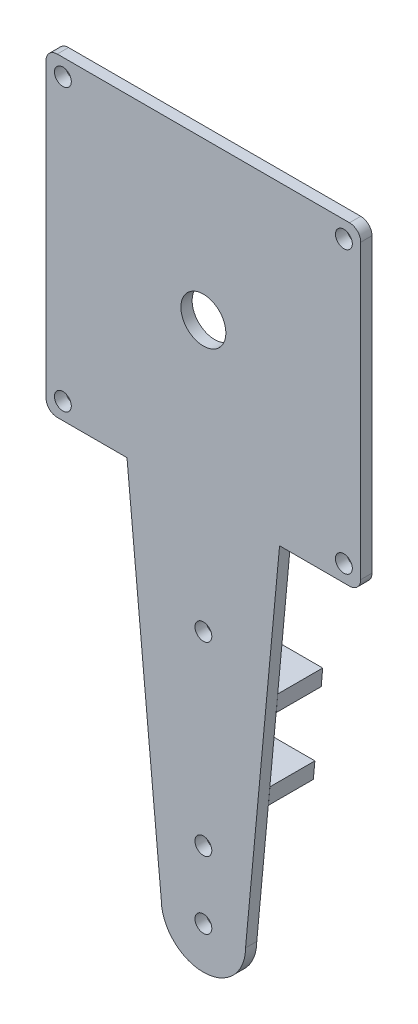
SolidWorks part; units mm, degrees
material "6061 Alloy"
ref_plane "Front Plane" through (0, 0, 0) normal (0, 0, 1) x (1, 0, 0)
ref_plane "Top Plane" through (0, 0, 0) normal (0, 1, 0) x (1, 0, 0)
ref_plane "Right Plane" through (0, 0, 0) normal (1, 0, 0) x (0, 0, -1)
sketch "Sketch2" plane through (0, 0, 0) normal (0, 0, 1) x (1, 0, 0)
  line L0 (-13.5937, -28) -> (-26, -28)
  line L1 (26, 28) -> (-26, 28)
  line L2 (28, 26) -> (28, -26)
  line L3 (26, -28) -> (13.5557, -28)
  line L4 (-28, 26) -> (-28, -26)
  line L5 (28, 28) -> (-28, -28) construction
  line L6 (28, -28) -> (-28, 28) construction
  line L13 (-7.5, -93) -> (7.5, -93)
  line L15 (-7.5, -93) -> (-13.5937, -28)
  line L16 (-14.976, -13.2559) -> (-12.375, -41) construction
  line L17 (7.5, -93) -> (13.5557, -28)
  circle A2 centre (25, 25) radius 1.5
  circle A3 centre (25, -25) radius 1.5
  circle A4 centre (-25, -25) radius 1.5
  circle A5 centre (-25, 25) radius 1.5
  arc A6 (28, 26) -> (26, 28) centre (26, 26) ccw
  arc A7 (28, -26) -> (26, -28) centre (26, -26) cw
  arc A8 (-26, -28) -> (-28, -26) centre (-26, -26) cw
  arc A9 (-28, 26) -> (-26, 28) centre (-26, 26) cw
  point P0 (0, 0)
  point P17 (0, 0)
  dimension "D1" = 56
  dimension "D2" = 56
  dimension "D3" = 25
  dimension "D4" = 3
  dimension "D6" = 2
  dimension "D7" = 2
  dimension "D8" = 65
  dimension "D9" = 15
  dimension "D10" = 7.5
  dimension "D5" = 4
extrude "Boss-Extrude1" add sketch "Sketch2" along normal blind 2
sketch "Sketch3" plane through (0, 0, 2) normal (0, 0, 1) x (1, 0, 0)
  circle A0 centre (0, 0) radius 4
  dimension "D1" = 8
extrude "Cut-Extrude1" cut sketch "Sketch3" against normal blind 10
sketch "Sketch4" plane through (0, 0, 0) normal (0, 0, -1) x (-1, 0, 0)
  line L0 (-11.2266, -53) -> (-10.9688, -56)
  line L1 (-7.5, -93) -> (-13.5557, -28) construction
  line L2 (11.25, -53) -> (-11.25, -53) construction
  line L3 (-10.9688, -56) -> (10.9687, -56)
  line L4 (10.9687, -56) -> (11.25, -53)
  line L5 (11.25, -53) -> (-11.2266, -53)
  line L6 (-9.8438, -68) -> (-9.5625, -71)
  line L7 (-9.5625, -71) -> (9.5625, -71)
  line L8 (13.5937, -28) -> (7.5, -93) construction
  line L9 (9.5625, -71) -> (7.5, -93) construction
  line L10 (9.5625, -71) -> (9.8437, -68)
  line L11 (9.8437, -68) -> (-9.8438, -68) construction
  line L12 (9.8437, -68) -> (-9.8438, -68)
extrude "Boss-Extrude2" add sketch "Sketch4" along normal blind 8
sketch "Sketch5" plane through (0, 0, 0) normal (0, 0, -1) x (-1, 0, 0)
  line L0 (0, 0) -> (0, -93) construction
  line L1 (7.5, -93) -> (-7.5, -93) construction
  circle A0 centre (0, -48) radius 1.5
  circle A1 centre (0, -81) radius 1.5
  dimension "D1" = 3
  dimension "D2" = 3
extrude "Cut-Extrude2" cut sketch "Sketch5" against normal up to surface (2 mm away) up to face at (4, 0, 2)
sketch "Sketch6" plane through (0, 0, 0) normal (0, 0, -1) x (-1, 0, 0)
  line L0 (7.5, -93) -> (-7.5, -93) construction
  circle A0 centre (0, -93) radius 7.5
extrude "Boss-Extrude3" add sketch "Sketch6" against normal up to surface (2 mm away) up to face at (1.5, -48, 2)
sketch "Sketch7" plane through (0, 0, 2) normal (0, 0, 1) x (1, 0, 0)
  line L0 (-7.5, -93) -> (7.5, -93) construction
  circle A0 centre (0, -93) radius 1.5
  dimension "D1" = 3
extrude "Cut-Extrude3" cut sketch "Sketch7" against normal up to surface (2 mm away) up to face at (-1.5, -81, 0)
